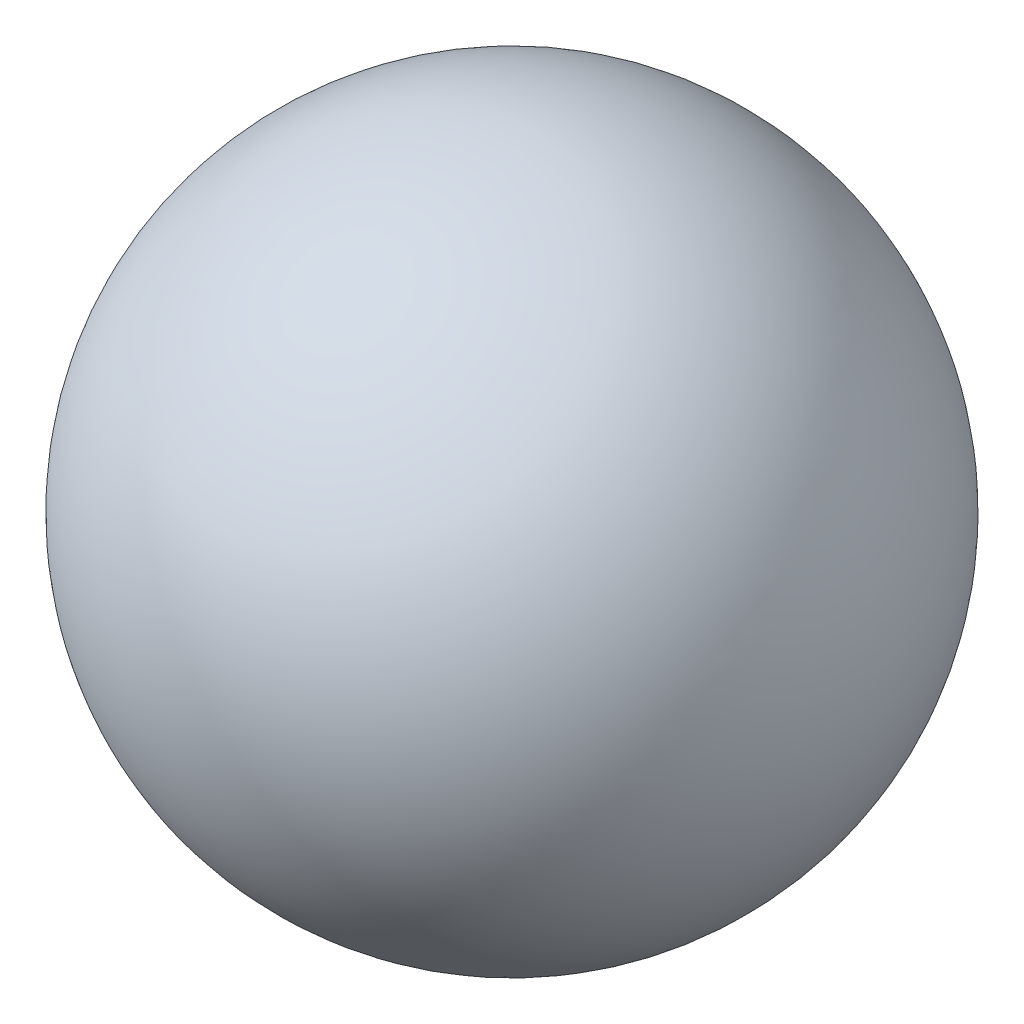
SolidWorks part; units mm, degrees
ref_plane "前视基准面" through (0, 0, 0) normal (0, 0, 1) x (1, 0, 0)
ref_plane "上视基准面" through (0, 0, 0) normal (0, 1, 0) x (1, 0, 0)
ref_plane "右视基准面" through (0, 0, 0) normal (1, 0, 0) x (0, 0, -1)
other "Configuration Table"
sketch "草图1" plane through (0, 0, 0) normal (0, 1, 0) x (1, 0, 0)
  line L0 (0, 113) -> (0, -113)
  arc A0 (0, -113) -> (0, 113) centre (0, 0) ccw
  dimension "D1" = 226
revolve "旋转1" add sketch "草图1" angle 360 about L0
